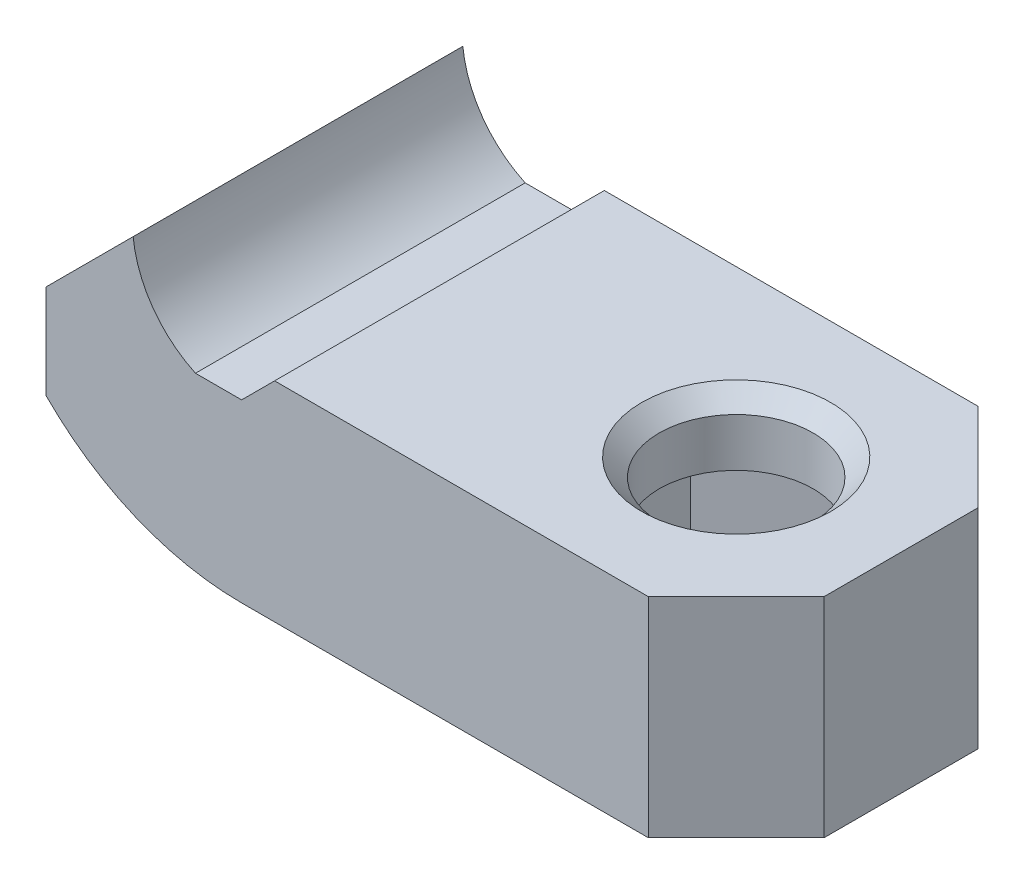
SolidWorks part; units mm, degrees
ref_plane "Alzado" through (0, 0, 0) normal (0, 0, 1) x (1, 0, 0)
ref_plane "Planta" through (0, 0, 0) normal (0, 1, 0) x (1, 0, 0)
ref_plane "Vista lateral" through (0, 0, 0) normal (1, 0, 0) x (0, 0, -1)
sketch "Croquis1" plane through (0, 0, 0) normal (0, 0, 1) x (1, 0, 0)
  line L0 (0, 0) -> (0, 5301.9663) construction
  line L1 (0, 0) -> (5301.9663, 0) construction
  line L2 (-4.8553, 4) -> (5297.111, 4) construction
  line L3 (0, 4) -> (-2.1, 4) construction
  line L4 (-8.9, 5.9678) -> (-8.9, -5295.9985) construction
  line L5 (-2.1, 7.8714) -> (-2.1, -5294.095) construction
  line L6 (-2.1, 4) -> (-2.1, 8.4) construction
  line L8 (-8.9, 4) -> (-8.9, -4) construction
  line L10 (-2.1, -4) -> (-2.1, -8.4) construction
  line L11 (0, -4) -> (-2.1, -4) construction
  line L12 (0, 4) -> (0, -4) construction
  line L13 (-4.5, -15.5102) -> (-4.5, 49984.4898) construction
  line L14 (-2.1, -8.4) -> (-4.5, -8.4) construction
  line L15 (-4.5, -8.4) -> (-8.9, -4) construction
  line L16 (-4.5, 8.4) -> (-8.9, 4) construction
  line L17 (-2.1, 8.4) -> (-4.5, 8.4) construction
  line L18 (17.5111, 5.5) -> (-49982.4889, 5.5) construction
  line L19 (23.2911, 8.5) -> (-49976.7089, 8.5) construction
  line L20 (-8.9, 4) -> (-4.9368, 7.9632)
  line L22 (-8.9, 4) -> (-8.9, -0.2772)
  line L23 (-2.1, 4) -> (0, 4)
  line L24 (0, 4) -> (0, -4)
  circle A0 centre (0, 8.5) radius 4.9659 construction
  circle A1 centre (0, 8.5) radius 12.5 construction
  arc A4 (0, -4) -> (-8.9, -0.2772) centre (0, 8.5) cw
  arc A5 (-2.1, 4) -> (-4.9368, 7.9632) centre (0, 8.5) cw
  point P17 (-8.9, 0)
  dimension "D1" = 8
  dimension "D2" = 6.8
  dimension "D3" = 2.1
  dimension "D4" = 8
  dimension "D5" = 16.8
  dimension "D6" = 2.4
  dimension "D7" = 1.5
  dimension "D8" = 3
extrude "Saliente-Extruir1" add sketch "Croquis1" along normal mid plane 15
sketch "Croquis6" plane through (0, 0, -7.5) normal (0, 0, -1) x (-1, 0, 0)
  line L0 (0, 0) -> (-50000, 0) construction
  line L1 (0, 0) -> (0, 50000) construction
  line L2 (-15, 0) -> (-15, 50000) construction
  line L3 (-3.8361, 5.5) -> (-50003.8361, 5.5) construction
  line L5 (0, 4) -> (-1.5, 5.5)
  line L6 (-1.5, 5.5) -> (-22.5, 5.5)
  line L7 (-22.5, 5.5) -> (-22.5, -4)
  line L8 (-22.5, -4) -> (0, -4)
  line L9 (0, -4) -> (0, 4)
  line L10 (0, 4) -> (2.1, 4) construction
  arc A0 (0, -4) -> (8.9, -0.2772) centre (0, 8.5) ccw construction
  point P14 (0, 4)
  point P19 (0, 4)
  point P21 (0, 0)
  point P22 (0, 0)
  point P23 (0, 0)
  point P24 (0, 0)
  point P25 (0, 0)
  point P26 (0, -4)
  point P30 (0, 0)
  point P31 (-22.5, -4)
  dimension "D1" = 15
  dimension "D2" = 1.5
  dimension "D3" = 15
  dimension "D4" = 45
extrude "Saliente-Extruir2" add sketch "Croquis6" against normal through all
sketch "Croquis7" plane through (0, 5.5, 0) normal (0, 1, 0) x (1, 0, 0)
  line L0 (0, 0) -> (50000, 0) construction
  line L1 (15, 0) -> (15, 50000) construction
  circle A0 centre (15, 0) radius 3.5
  dimension "D2" = 7
  dimension "D1" = 15
extrude "Cortar-Extruir4" cut sketch "Croquis7" against normal through all
sketch "Croquis8" plane through (0, 5.5, 0) normal (0, 1, 0) x (1, 0, 0)
  line L1 (15, 5.658) -> (10.1, 2.829)
  line L2 (10.1, 2.829) -> (10.1, -2.829)
  line L3 (10.1, -2.829) -> (15, -5.658)
  line L4 (15, -5.658) -> (19.9, -2.829)
  line L5 (19.9, -2.829) -> (19.9, 2.829)
  line L6 (19.9, 2.829) -> (15, 5.658)
  circle A0 centre (15, 0) radius 4.9 construction
  dimension "D1" = 9.8
extrude "Cortar-Extruir5" cut sketch "Croquis8" against normal blind 10 from offset 3 offset against normal yes
chamfer "Chaflán4" distance 4 angle 45 2 edges at (22.5, 0.75, -7.5) (22.5, 0.75, 7.5)
chamfer "Chaflán5" distance 0.8 angle 45 7 edges at (10.1, -4, 0) (12.55, -4, 4.2435) (17.45, -4, 4.2435) (19.9, -4, 0) (17.45, -4, -4.2435) (12.55, -4, -4.2435) (11.5, 5.5, 0)
